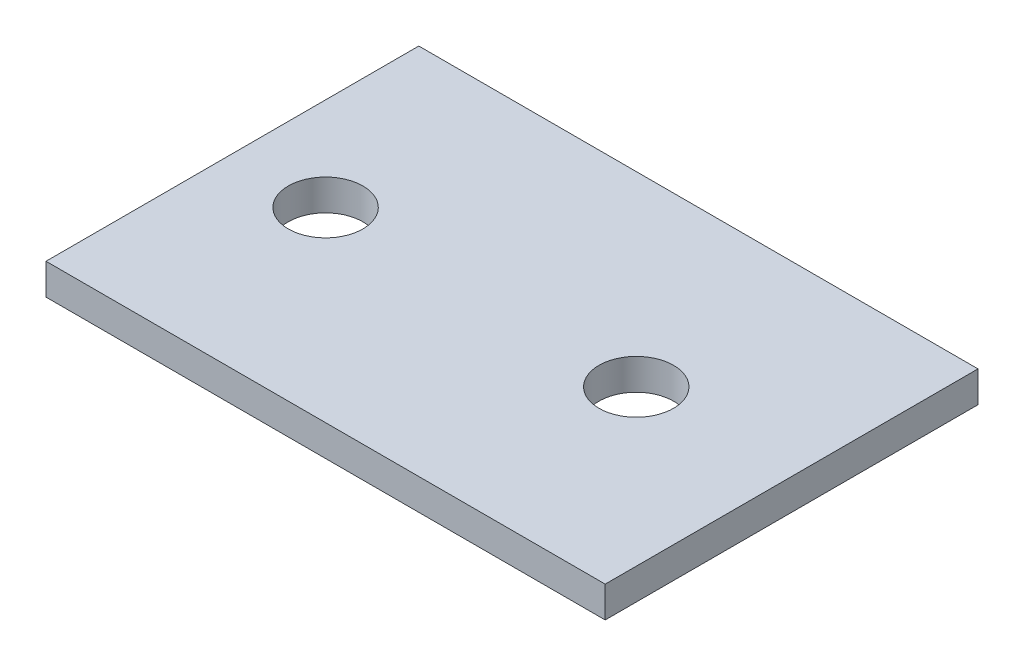
SolidWorks part; units mm, degrees
material "Plain Carbon Steel"
ref_plane "Front Plane" through (0, 0, 0) normal (0, 0, 1) x (1, 0, 0)
ref_plane "Top Plane" through (0, 0, 0) normal (0, 1, 0) x (1, 0, 0)
ref_plane "Right Plane" through (0, 0, 0) normal (1, 0, 0) x (0, 0, -1)
sketch "Sketch4" plane through (0, 0, 0) normal (0, 1, 0) x (1, 0, 0)
  line L0 (0, 0) -> (0, 45.7031) construction
  line L1 (-45, -30) -> (45, -30)
  line L2 (-45, -30) -> (-45, 30)
  line L3 (-45, 30) -> (45, 30)
  line L4 (45, -30) -> (45, 30)
  line L5 (-45, -30) -> (45, 30) construction
  line L6 (-45, 30) -> (45, -30) construction
  circle A0 centre (-30, 0) radius 6
  circle A2 centre (20, 0) radius 6
  point P0 (0, 0)
  point P12 (0, 0)
  point P13 (0, 0)
  point P14 (17.1542, 0)
  dimension "D2" = 15
  dimension "D3" = 12
  dimension "D5" = 50
  dimension "D1" = 90
  dimension "D4" = 60
extrude "Boss-Extrude1" add sketch "Sketch4" along normal mid plane 5
